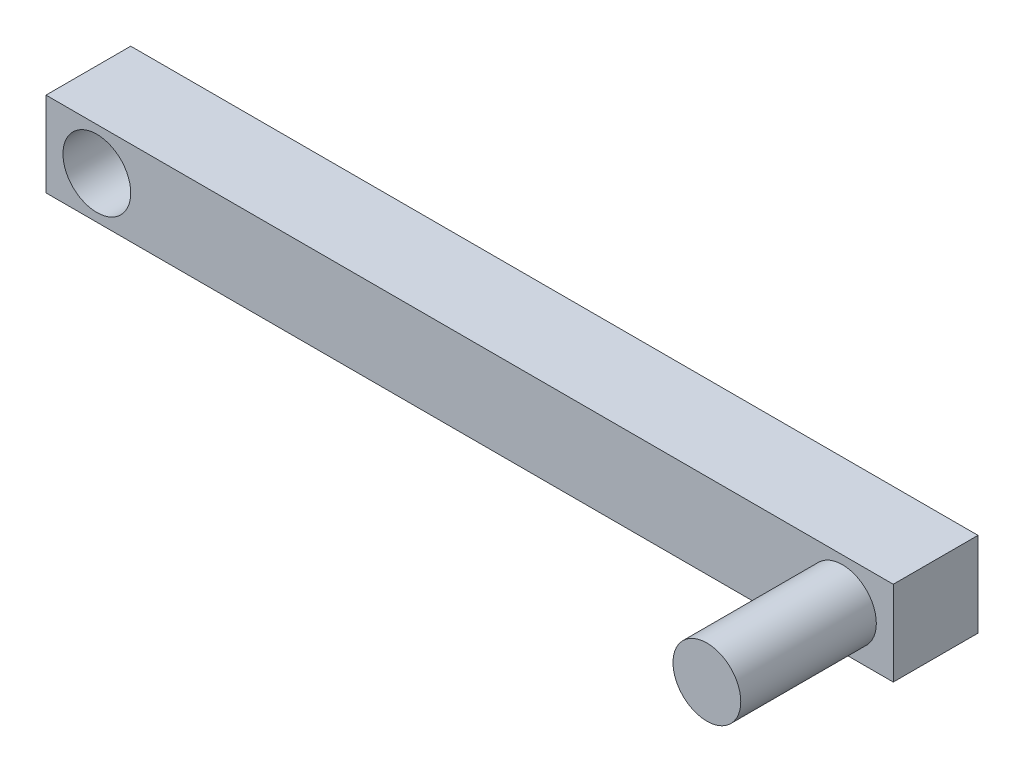
SolidWorks part; units mm, degrees
ref_plane "前视基准面" through (0, 0, 0) normal (0, 0, 1) x (1, 0, 0)
ref_plane "上视基准面" through (0, 0, 0) normal (0, 1, 0) x (1, 0, 0)
ref_plane "右视基准面" through (0, 0, 0) normal (1, 0, 0) x (0, 0, -1)
sketch "草图2" plane through (0, 0, 0) normal (0, 0, 1) x (1, 0, 0)
  line L1 (-41.04, 5) -> (8.96, 5)
  line L2 (-41.04, 5) -> (-41.04, 0)
  line L3 (-41.04, 0) -> (8.96, 0)
  line L4 (8.96, 5) -> (8.96, 0)
  dimension "D1" = 5
  dimension "D2" = 50
extrude "凸台-拉伸1" add sketch "草图2" along normal blind 5
sketch "草图3" plane through (0, 0, 5) normal (0, 0, 1) x (1, 0, 0)
  line L0 (-41.04, 0) -> (8.96, 0) construction
  line L1 (-41.04, 5) -> (-41.04, 0) construction
  circle A0 centre (-38.04, 2.5) radius 2
  dimension "D2" = 4
  dimension "D1" = 2.5
  dimension "D3" = 3
extrude "切除-拉伸1" cut sketch "草图3" against normal blind 5
sketch "草图4" plane through (0, 0, 5) normal (0, 0, 1) x (1, 0, 0)
  line L0 (-41.04, 0) -> (8.96, 0) construction
  line L1 (8.96, 0) -> (8.96, 5) construction
  circle A0 centre (5.96, 2.5) radius 2
  dimension "D2" = 4
  dimension "D1" = 2.5
  dimension "D3" = 3
extrude "凸台-拉伸2" add sketch "草图4" along normal blind 8
